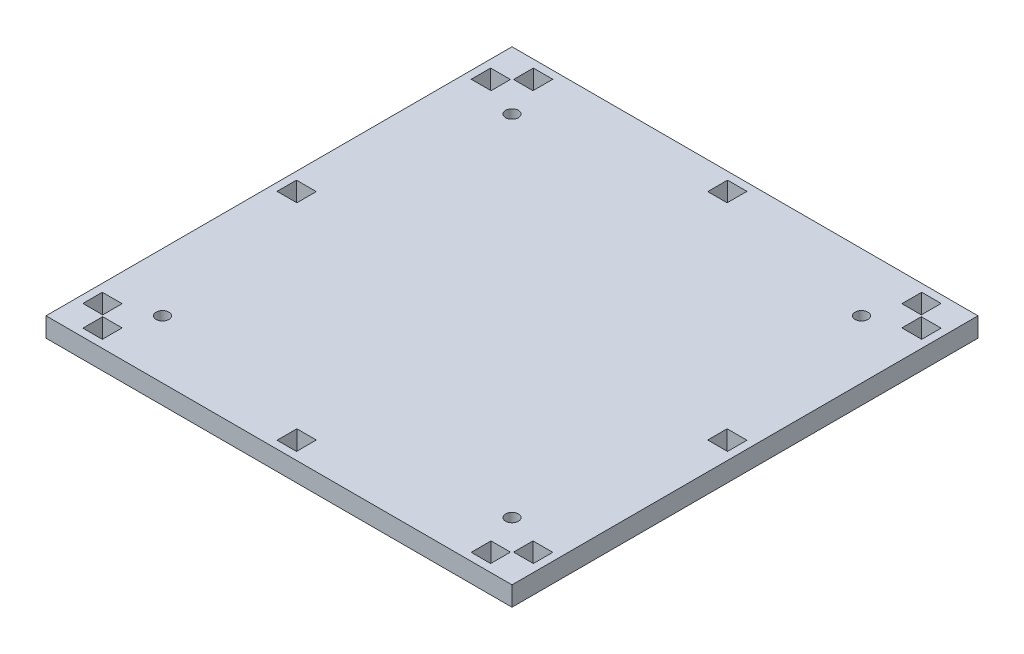
SolidWorks part; units mm, degrees
ref_plane "Front" through (0, 0, 0) normal (0, 0, 1) x (1, 0, 0)
ref_plane "Top" through (0, 0, 0) normal (0, 1, 0) x (1, 0, 0)
ref_plane "Right" through (0, 0, 0) normal (1, 0, 0) x (0, 0, -1)
sketch "Sketch1" plane through (0, 0, 0) normal (0, 1, 0) x (1, 0, 0)
  line L1 (-60, -60) -> (60, -60)
  line L2 (-60, -60) -> (-60, 60)
  line L3 (-60, 60) -> (60, 60)
  line L4 (60, -60) -> (60, 60)
  line L5 (-60, -60) -> (60, 60) construction
  line L6 (-60, 60) -> (60, -60) construction
  point P0 (0, 0)
  dimension "D1" = 120
  dimension "D2" = 120
extrude "Boss-Extrude1" add sketch "Sketch1" along normal blind 5
hole_wizard "Ø3.3 (3.3) Diameter Hole1" positions "Sketch3" profile "Sketch2" hole size "Ø3.3" standard "ANSI Metric" end condition through all
sketch "Sketch3" plane through (0, 5, 0) normal (0, 1, 0) x (1, 0, 0)
  line L1 (-45, -45) -> (45, -45)
  line L2 (-45, -45) -> (-45, 45)
  line L3 (-45, 45) -> (45, 45)
  line L4 (45, -45) -> (45, 45)
  line L5 (-45, -45) -> (45, 45) construction
  line L6 (-45, 45) -> (45, -45) construction
  line L7 (-60, 60) -> (-60, -60) construction
  line L8 (-60, -60) -> (60, -60) construction
  point P0 (-45, 45)
  point P2 (45, 45)
  point P4 (45, -45)
  point P6 (-45, -45)
  dimension "D1" = 90
  dimension "D2" = 90
  dimension "D3" = 15
  dimension "D4" = 15
sketch "Sketch2" plane through (-45, 5, -45) normal (1, 0, 0) x (0, 0, 1)
  line L0 (0, 0) -> (0, 5)
  line L1 (0, 5) -> (1.65, 5)
  line L2 (1.65, 5) -> (1.65, 0)
  line L5 (1.65, 0) -> (0, 0)
  line L11 (0, -6.35) -> (0, 107.95) construction
  dimension "Thru Hole Dia." = 3.3
  dimension "Thru Hole Depth" = 5
sketch "Sketch5" plane through (0, 5, 0) normal (0, 1, 0) x (1, 0, 0)
  line L0 (-60, 60) -> (-60, -60) construction
  line L1 (-58, 52.5) -> (-52.9, 52.5)
  line L2 (-58, 52.5) -> (-58, 47.5)
  line L3 (-58, 47.5) -> (-52.9, 47.5)
  line L4 (-52.9, 52.5) -> (-52.9, 47.5)
  line L5 (-58, -47.5) -> (-52.9, -47.5)
  line L6 (-58, -47.5) -> (-58, -52.5)
  line L7 (-58, -52.5) -> (-52.9, -52.5)
  line L8 (-52.9, -47.5) -> (-52.9, -52.5)
  line L9 (-52.5, -52.9) -> (-47.5, -52.9)
  line L10 (-52.5, -52.9) -> (-52.5, -58)
  line L11 (-52.5, -58) -> (-47.5, -58)
  line L12 (-47.5, -52.9) -> (-47.5, -58)
  line L13 (52.5, -52.9) -> (47.5, -52.9)
  line L14 (52.5, -52.9) -> (52.5, -58)
  line L15 (52.5, -58) -> (47.5, -58)
  line L16 (47.5, -52.9) -> (47.5, -58)
  line L17 (-52.5, 58) -> (-47.5, 58)
  line L18 (-52.5, 58) -> (-52.5, 52.9)
  line L19 (-52.5, 52.9) -> (-47.5, 52.9)
  line L20 (-47.5, 58) -> (-47.5, 52.9)
  line L21 (52.5, 58) -> (47.5, 58)
  line L22 (52.5, 58) -> (52.5, 52.9)
  line L23 (52.5, 52.9) -> (47.5, 52.9)
  line L24 (47.5, 58) -> (47.5, 52.9)
  line L25 (52.9, 52.5) -> (58, 52.5)
  line L26 (52.9, 52.5) -> (52.9, 47.5)
  line L27 (52.9, 47.5) -> (58, 47.5)
  line L28 (58, 52.5) -> (58, 47.5)
  line L29 (52.9, -47.5) -> (58, -47.5)
  line L30 (52.9, -47.5) -> (52.9, -52.5)
  line L31 (52.9, -52.5) -> (58, -52.5)
  line L32 (58, -47.5) -> (58, -52.5)
  line L33 (60, 60) -> (-60, 60) construction
  line L34 (60, -60) -> (60, 60) construction
  line L35 (-60, -60) -> (60, -60) construction
  line L37 (-58, 2.5) -> (-52.9, 2.5)
  line L38 (-58, 2.5) -> (-58, -2.5)
  line L39 (-58, -2.5) -> (-52.9, -2.5)
  line L40 (-52.9, 2.5) -> (-52.9, -2.5)
  line L41 (-2.5, 58) -> (2.5, 58)
  line L42 (-2.5, 58) -> (-2.5, 52.9)
  line L43 (-2.5, 52.9) -> (2.5, 52.9)
  line L44 (2.5, 58) -> (2.5, 52.9)
  line L45 (-2.5, -52.9) -> (2.5, -52.9)
  line L46 (-2.5, -52.9) -> (-2.5, -58)
  line L47 (-2.5, -58) -> (2.5, -58)
  line L48 (2.5, -52.9) -> (2.5, -58)
  line L49 (52.9, 2.5) -> (58, 2.5)
  line L50 (52.9, 2.5) -> (52.9, -2.5)
  line L51 (52.9, -2.5) -> (58, -2.5)
  line L52 (58, 2.5) -> (58, -2.5)
  dimension "D1" = 2
  dimension "D2" = 95
  dimension "D3" = 105
  dimension "D4" = 7.5
  dimension "D5" = 5.1
  dimension "D6" = 2
  dimension "D7" = 5.1
  dimension "D8" = 2
  dimension "D9" = 5.1
  dimension "D10" = 2
  dimension "D11" = 5.1
  dimension "D12" = 95
  dimension "D13" = 105
  dimension "D14" = 7.5
  dimension "D15" = 5
  dimension "D16" = 45
  dimension "D17" = 5
  dimension "D18" = 45
extrude "Cut-Extrude1" cut sketch "Sketch5" against normal through all
